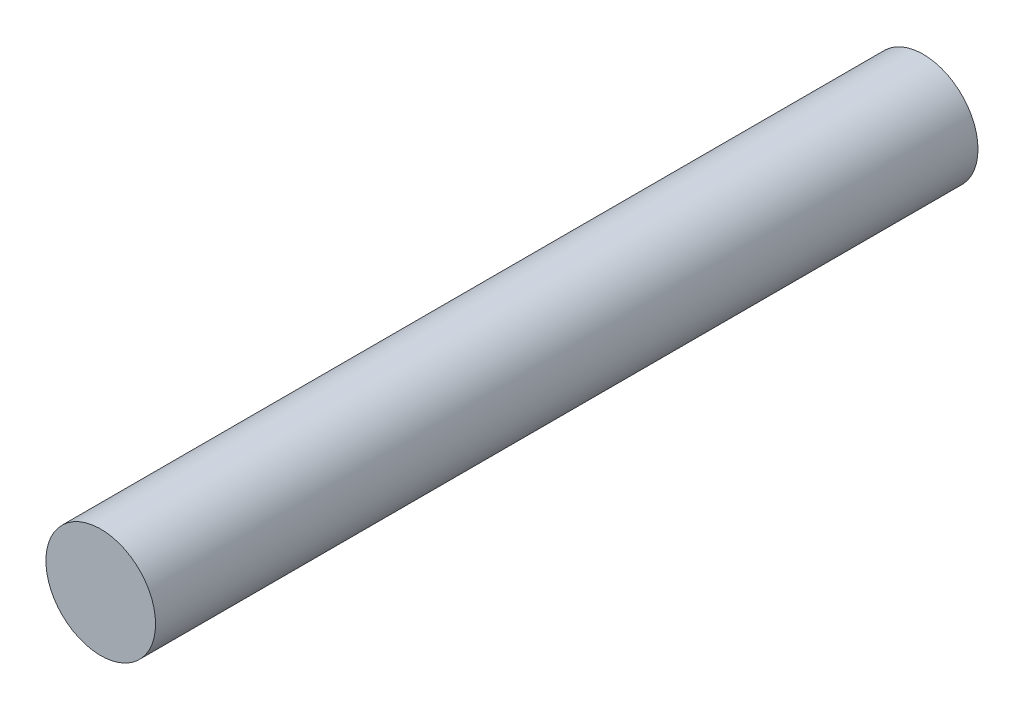
SolidWorks part; units mm, degrees
ref_plane "Front Plane" through (0, 0, 0) normal (0, 0, 1) x (1, 0, 0)
ref_plane "Top Plane" through (0, 0, 0) normal (0, 1, 0) x (1, 0, 0)
ref_plane "Right Plane" through (0, 0, 0) normal (1, 0, 0) x (0, 0, -1)
sketch "Sketch1" plane through (0, 0, 0) normal (0, 0, 1) x (1, 0, 0)
  circle A0 centre (0, 0) radius 1
  dimension "D1" = 2
extrude "Boss-Extrude1" add sketch "Sketch1" along normal blind 15
